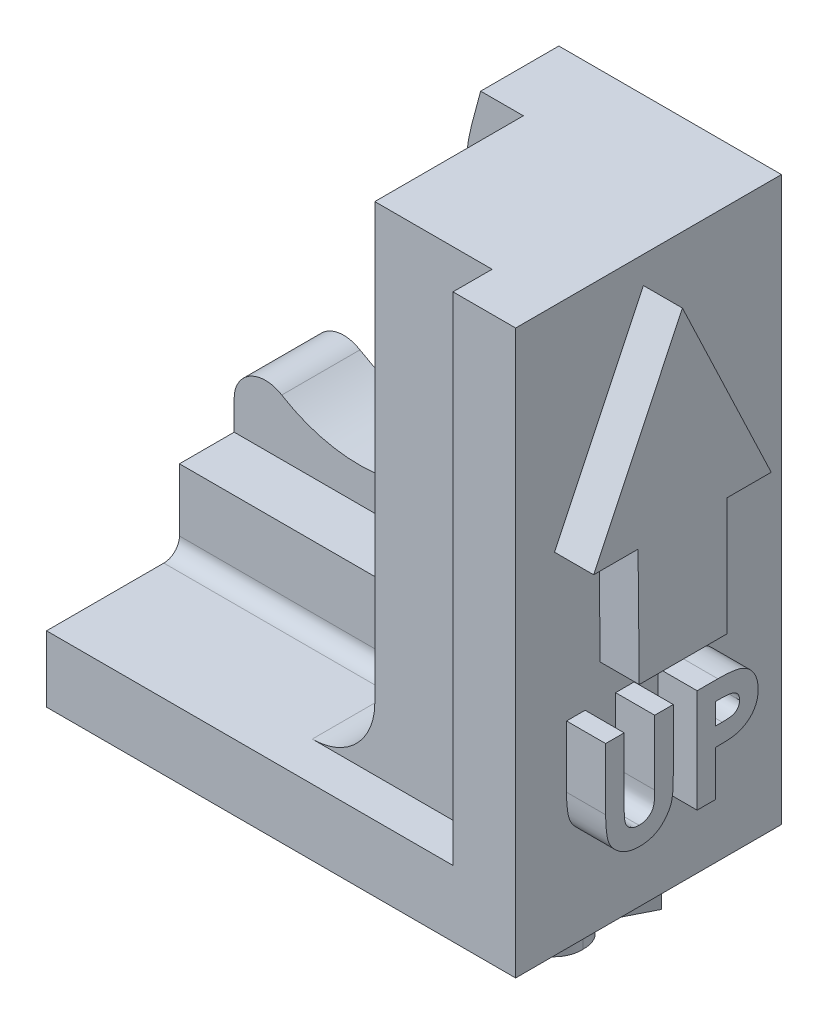
SolidWorks part; units mm, degrees
ref_plane "Front Plane" through (0, 0, 0) normal (0, 0, 1) x (1, 0, 0)
ref_plane "Top Plane" through (0, 0, 0) normal (0, 1, 0) x (1, 0, 0)
ref_plane "Right Plane" through (0, 0, 0) normal (1, 0, 0) x (0, 0, -1)
sketch "Sketch2" plane through (0, 0, 0) normal (0, 0, 1) x (1, 0, 0)
  line L1 (-15, -18) -> (15, -18)
  line L2 (-15, -18) -> (-15, 18)
  line L3 (-15, 18) -> (15, 18)
  line L4 (15, -18) -> (15, 18)
  line L5 (-15, -18) -> (15, 18) construction
  line L6 (-15, 18) -> (15, -18) construction
  point P0 (0, 0)
  dimension "D1" = 36
  dimension "D2" = 30
extrude "Boss-Extrude1" add sketch "Sketch2" along normal blind 17
sketch "Sketch3" plane through (0, 0, 17) normal (0, 0, 1) x (1, 0, 0)
  line L3 (-1.006, -12.7696) -> (-45.006, -12.7696) construction
  line L4 (-1.006, -12.7696) -> (-45.006, -12.7696) construction
  line L5 (9.994, 11.917) -> (9.994, -6.083) construction
  line L6 (9.994, 11.917) -> (9.994, -6.083) construction
  line L7 (10.994, -13.7696) -> (10.994, 20.7951)
  line L8 (9.994, -12.7696) -> (-15, -12.7696) construction
  line L9 (9.994, -12.7696) -> (9.994, 19.7951) construction
  line L10 (9.994, 19.7951) -> (-15, 19.7951) construction
  line L11 (-15, -12.7696) -> (-15, 19.7951) construction
  line L12 (10.994, 20.7951) -> (-16, 20.7951)
  line L13 (-16, -13.7696) -> (-16, 20.7951)
  line L14 (10.994, -13.7696) -> (-16, -13.7696)
  dimension "D1" = 1
extrude "Cut-Extrude1" cut sketch "Sketch3" against normal blind 12
sketch "Sketch4" plane through (0, 0, 0) normal (0, 0, -1) x (-1, 0, 0)
  line L0 (7.006, -32.9084) -> (7.006, 38.7423) construction
  line L1 (7.006, 2.917) -> (-3.7911, 43.2122) construction
  line L2 (1.2533, 10.4771) -> (-7.5479, 43.3235)
  line L3 (15, 18) -> (15, 8.0498)
  line L4 (15, 18) -> (15, -18) construction
  line L5 (15, 18) -> (-0.7625, 18)
  circle A0 centre (7.006, 2.917) radius 3 construction
  circle A1 centre (7.006, 2.917) radius 3 construction
  circle A3 centre (7.006, 2.917) radius 9.5
  point P8 (7.006, 2.917)
  line M7 (15, -18) -> (15, 18)
  line M8 (15, 18) -> (-15, 18)
  dimension "D1" = 15
  dimension "D2" = 3.6
extrude "Cut-Extrude2" cut sketch "Sketch4" against normal blind 10 contours A3 L2 M7 M8 | A3 M7
fillet "Fillet1" radius 11 1 edges at (-1.2533, 10.4771, 2.5)
fillet "Fillet2" radius 2 1 edges at (-15, -2.2159, 2.5)
sketch "Sketch5" plane through (10.994, 0, 0) normal (-1, 0, 0) x (0, 0, 1)
  line L0 (5, 18) -> (17, 18) construction
  line L1 (5, -13.7696) -> (14.5, -13.7696)
  line L2 (5, -13.7696) -> (5, 18)
  line L3 (5, 18) -> (14.5, 18)
  line L4 (14.5, -13.7696) -> (14.5, 18)
  line L5 (17, -13.7696) -> (17, 18) construction
  dimension "D1" = 2.5
extrude "Boss-Extrude2" add sketch "Sketch5" along normal blind 7.5
sketch "Sketch6" plane through (0, 0, 5) normal (0, 0, 1) x (1, 0, 0)
  line L0 (3.494, 18) -> (3.494, -13.7696) construction
  line L1 (-15, -13.7696) -> (3.494, -13.7696)
  line L2 (-15, -13.7696) -> (-15, -8.7696)
  line L3 (-15, -8.7696) -> (3.494, -8.7696)
  line L4 (3.494, -13.7696) -> (3.494, -8.7696)
  dimension "D1" = 5
extrude "Boss-Extrude3" add sketch "Sketch6" along normal blind 3.5
fillet "Fillet3" radius 4 1 edges at (3.494, -13.7696, 11.5)
fillet "Fillet4" radius 1 3 edges at (3.494, -9.2696, 8.5) (2.3224, -12.598, 8.5) (-7.753, -13.7696, 8.5)
sketch "Sketch7" plane through (15, 0, 0) normal (1, 0, 0) x (0, 0, -1)
  line L0 (-11.596, -3.1978) -> (-5.9937, -3.1978)
  line L1 (-5.9937, -3.1978) -> (-5.9937, 4.3371)
  line L2 (-5.9937, 4.3371) -> (-3.1552, 4.3371)
  line L3 (-3.1552, 4.3371) -> (-8.8323, 16.2698)
  line L4 (-8.8323, 16.2698) -> (-14.5094, 4.3371)
  line L5 (-14.5094, 4.3371) -> (-11.6708, 4.3371)
  line L6 (-11.6708, 4.3371) -> (-11.596, -3.1978)
  text T0 "UP" font "Century Gothic" height in points 25
  point P6 (0, 0)
extrude "Boss-Extrude4" add sketch "Sketch7" along normal blind 2.5
sketch "Sketch8" plane through (0, -18, 0) normal (0, -1, 0) x (1, 0, 0)
  line L0 (-15, 17) -> (-15, 0) construction
  text T0 "FEMUR" font "Century Gothic" height in points 25
  point P1 (3.689, 5.8593)
  point P2 (-13.7225, 2.5285)
  point P3 (0, 0)
  point P4 (-15, 6.0385)
  point P7 (0, 0)
extrude "Boss-Extrude5" add sketch "Sketch8" along normal blind 2.5
